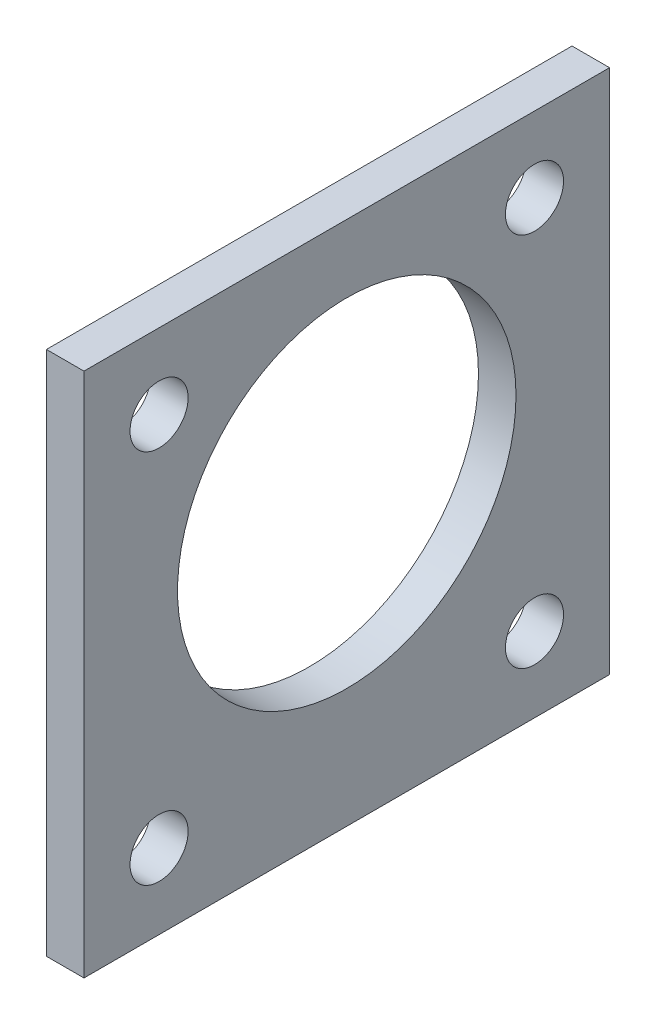
SolidWorks part; units mm, degrees
ref_plane "Front" through (0, 0, 0) normal (0, 0, 1) x (1, 0, 0)
ref_plane "Top" through (0, 0, 0) normal (0, 1, 0) x (1, 0, 0)
ref_plane "Right" through (0, 0, 0) normal (1, 0, 0) x (0, 0, -1)
sketch "Sketch1" plane through (0, 0, 0) normal (1, 0, 0) x (0, 0, -1)
  line L1 (-22.225, -22.225) -> (22.225, -22.225)
  line L2 (-22.225, -22.225) -> (-22.225, 22.225)
  line L3 (-22.225, 22.225) -> (22.225, 22.225)
  line L4 (22.225, -22.225) -> (22.225, 22.225)
  line L5 (-22.225, -22.225) -> (22.225, 22.225) construction
  line L6 (-22.225, 22.225) -> (22.225, -22.225) construction
  point P0 (0, 0)
  dimension "D1" = 44.45
extrude "Boss-Extrude1" add sketch "Sketch1" along normal blind 3.175
sketch "Sketch2" plane through (3.175, 0, 0) normal (1, 0, 0) x (0, 0, -1)
  line L0 (22.225, 22.225) -> (-22.225, 22.225) construction
  line L1 (22.225, -22.225) -> (22.225, 22.225) construction
  line L2 (-15.875, -15.875) -> (15.875, -15.875) construction
  line L3 (-15.875, -15.875) -> (-15.875, 15.875) construction
  line L4 (-15.875, 15.875) -> (15.875, 15.875) construction
  line L5 (15.875, -15.875) -> (15.875, 15.875) construction
  line L6 (-15.875, -15.875) -> (15.875, 15.875) construction
  line L7 (-15.875, 15.875) -> (15.875, -15.875) construction
  line L8 (-22.225, 10.8326) -> (22.225, 10.8326) construction
  line L9 (-22.225, 22.225) -> (-22.225, -22.225) construction
  circle A0 centre (0, 2.175) radius 14.3129
  circle A1 centre (-15.875, 15.875) radius 2.4574
  circle A2 centre (15.875, 15.875) radius 2.4574
  circle A3 centre (15.875, -15.875) radius 2.4574
  circle A4 centre (-15.875, -15.875) radius 2.4574
  point P5 (0, 0)
  point P17 (0, 10.8326)
  dimension "D2" = 28.6258
  dimension "D3" = 4.9149
  dimension "D1" = 20.05
  dimension "D4" = 6.35
extrude "Cut-Extrude1" cut sketch "Sketch2" against normal through all
